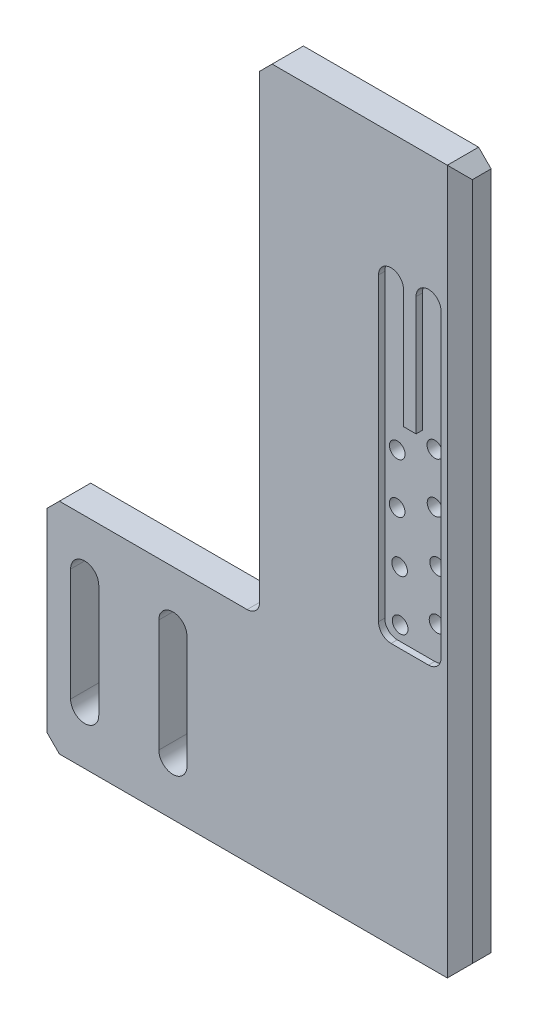
SolidWorks part; units mm, degrees
ref_plane "Front Plane" through (0, 0, 0) normal (0, 0, 1) x (1, 0, 0)
ref_plane "Top Plane" through (0, 0, 0) normal (0, 1, 0) x (1, 0, 0)
ref_plane "Right Plane" through (0, 0, 0) normal (1, 0, 0) x (0, 0, -1)
sketch "Sketch1" plane through (0, 0, 0) normal (0, 0, 1) x (1, 0, 0)
  line L0 (-25, 62.9394) -> (7, 62.9394)
  line L1 (7, 62.9394) -> (7, -49.5606)
  line L2 (7, -49.5606) -> (-59, -49.5606)
  line L3 (-59, -49.5606) -> (-59, -14.5606)
  line L4 (-59, -14.5606) -> (-25, -14.5606)
  line L5 (-25, -14.5606) -> (-25, 62.9394)
  line L8 (-55.2093, -23.0606) -> (-55.2093, -41.0606)
  line L10 (-50.7093, -23.0606) -> (-50.7093, -41.0606)
  line L12 (-41.1088, -23.0606) -> (-41.1088, -41.0606)
  line L14 (-36.6088, -23.0606) -> (-36.6088, -41.0606)
  arc A0 (-50.7093, -23.0606) -> (-55.2093, -23.0606) centre (-52.9593, -23.0606) ccw
  arc A1 (-36.6088, -23.0606) -> (-41.1088, -23.0606) centre (-38.8588, -23.0606) ccw
  arc A2 (-41.1088, -41.0606) -> (-36.6088, -41.0606) centre (-38.8588, -41.0606) ccw
  arc A3 (-55.2093, -41.0606) -> (-50.7093, -41.0606) centre (-52.9593, -41.0606) ccw
  dimension "D1" = 32
  dimension "D2" = 34
  dimension "D3" = 35
  dimension "D4" = 112.5
  dimension "D5" = 18
  dimension "D6" = 4.5
  dimension "D7" = 18
extrude "Boss-Extrude1" add sketch "Sketch1" along normal blind 5
sketch "Sketch5" plane through (0, 0, 5) normal (0, 0, 1) x (1, 0, 0)
  line L0 (-2, 42.2498) -> (-2, 23.2498)
  line L2 (-6, 42.2498) -> (-6, -7.7502)
  line L3 (-6, -7.7502) -> (4, -7.7502)
  line L4 (4, 42.2498) -> (4, -7.7502)
  line L5 (-2, 23.2498) -> (0, 23.2498)
  line L6 (0, 23.2498) -> (0, 42.2498)
  arc A0 (-2, 42.2498) -> (-6, 42.2498) centre (-4, 42.2498) ccw
  arc A1 (4, 42.2498) -> (0, 42.2498) centre (2, 42.2498) ccw
  dimension "D1" = 4
  dimension "D2" = 4
  dimension "D3" = 19
  dimension "D4" = 2
  dimension "D5" = 50
extrude "Cut-Extrude1" cut sketch "Sketch5" against normal blind 1
fillet "Fillet1" radius 2 2 edges at (-6, -7.7502, 4.5) (4, -7.7502, 4.5)
hole_wizard "M3x0.5 Tapped Hole1" positions "Sketch6" profile "Sketch7" tap size "M3x0.5" standard "ANSI Metric" end condition through all
sketch "Sketch6" plane through (0, 0, 4) normal (0, 0, 1) x (1, 0, 0)
  line L0 (4, -5.7502) -> (4, 42.2498) construction
  line L1 (-6, 42.2498) -> (-6, -5.7502) construction
  point P0 (-4, 18.5424)
  point P2 (2, 21.6307)
  point P4 (2.0349, 13.6308)
  point P6 (-4.0254, 10.5425)
  point P8 (2.452, 5.6308)
  point P10 (-3.6302, 2.5522)
  point P12 (2.3582, -2.3687)
  point P14 (-3.5363, -5.4472)
  point P21 (1.8501, 9.16)
  point P22 (0, 0)
  point P23 (0, 0)
  point P24 (1.8501, 1.16)
  point P25 (1.8501, 1.16)
  point P26 (1.8501, 25.018)
  point P27 (2.2127, -4.2602)
  point P28 (1.7538, 21.6307)
  point P29 (0, 0)
  point P30 (0, 0)
  point P31 (-3.0584, -5.7724)
  point P32 (-3.4901, 18.5424)
  dimension "D1" = 8
  dimension "D2" = 8
  dimension "D3" = 8
  dimension "D4" = 8
  dimension "D5" = 8
  dimension "D6" = 8
  dimension "D7" = 2
  dimension "D8" = 2
sketch "Sketch7" plane through (-4, 18.5424, 4) normal (1, 0, 0) x (0, -1, 0)
  line L0 (0, 0) -> (0, 4)
  line L1 (0, 4) -> (1.25, 4)
  line L2 (1.25, 4) -> (1.25, 0)
  line L5 (1.25, 0) -> (0, 0)
  line L11 (0, -6.35) -> (0, 107.95) construction
  dimension "Thru Tap Drill Dia." = 2.5
  dimension "Thru Tap Drill Depth" = 4
cosmetic thread "Hole Thread1" parameters "D2"=3
cosmetic thread "Hole Thread2" parameters "D2"=3
cosmetic thread "Hole Thread3" parameters "D2"=3
cosmetic thread "Hole Thread4" parameters "D2"=3
cosmetic thread "Hole Thread5" parameters "D2"=3
cosmetic thread "Hole Thread6" parameters "D2"=3
cosmetic thread "Hole Thread7" parameters "D2"=3
cosmetic thread "Hole Thread8" parameters "D2"=3
chamfer "Chamfer1" distance 2 angle 45 6 edges at (7, 62.9394, 2.5) (7, 6.6894, 5) (7, -49.5606, 2.5) (-59, -49.5606, 2.5) (-59, -14.5606, 2.5) (-25, 62.9394, 2.5)
fillet "Fillet2" radius 2 1 edges at (-25, -14.5606, 2.5)
